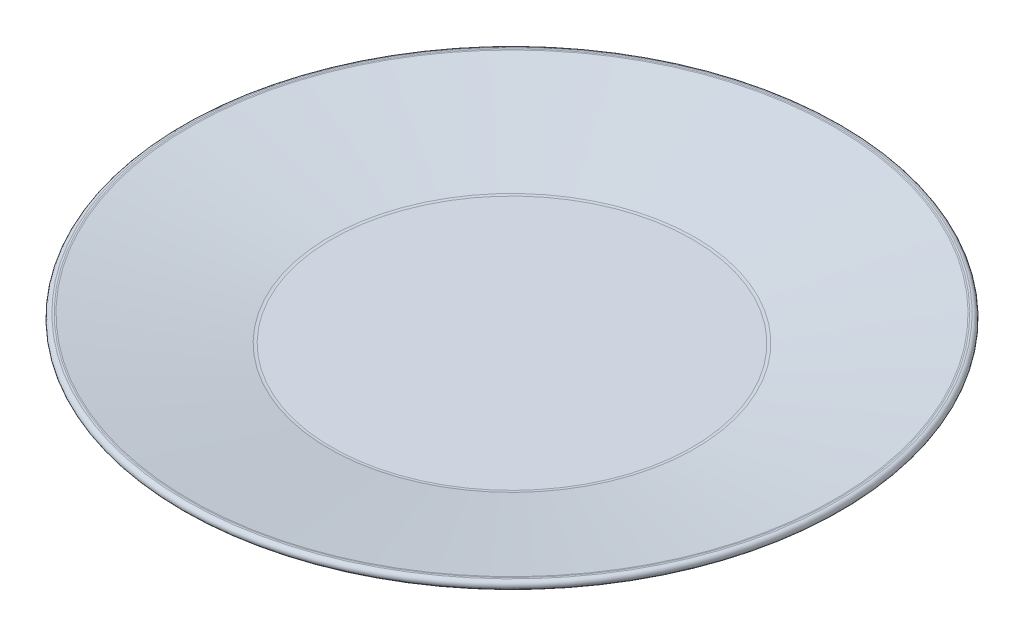
SolidWorks part; units mm, degrees
material "Ceramic Porcelain"
ref_plane "Front Plane" through (0, 0, 0) normal (0, 0, 1) x (1, 0, 0)
ref_plane "Top Plane" through (0, 0, 0) normal (0, 1, 0) x (1, 0, 0)
ref_plane "Right Plane" through (0, 0, 0) normal (1, 0, 0) x (0, 0, -1)
sketch "ProfileS" plane through (0, 0, 0) normal (0, 0, 1) x (1, 0, 0)
  line L0 (0, 0) -> (51.9562, 0)
  line L1 (53.2226, 0.1155) -> (94.0171, 7.6198)
  line L2 (0, 0) -> (0, 10) construction
  line L3 (0, 10) -> (106.9562, 10) construction
  line L4 (0, 2.5) -> (51.9562, 2.5)
  line L5 (52.7703, 2.5743) -> (92.9584, 9.967)
  line L6 (0, 2.5) -> (0, 0)
  line L7 (93.8, 10) -> (93.3202, 10)
  line L8 (53.2226, 0.1155) -> (106.9562, 10) construction
  line L9 (52.7703, 2.5743) -> (106.5039, 12.4587) construction
  line L10 (106.9562, 10) -> (106.9562, 0) construction
  line L11 (106.9562, 0) -> (0, 0) construction
  line L12 (94.0171, 7.6198) -> (106.9562, 10) construction
  line L13 (95, 10) -> (95, 0) construction
  arc A0 (53.2226, 0.1155) -> (51.9562, 0) centre (51.9562, 7) cw
  arc A1 (52.7703, 2.5743) -> (51.9562, 2.5) centre (51.9562, 7) cw
  arc A2 (94.0171, 7.6198) -> (93.8, 10) centre (93.8, 8.8) ccw
  arc A3 (93.3202, 10) -> (92.9584, 9.967) centre (93.3202, 8) ccw
  point P18 (93.1378, 10)
  dimension "SWStartRadius" = 7
  dimension "D1" = 1.2
  dimension "D2" = 2
  dimension "Height" = 10
  dimension "SlantedWallWidth" = 55
  dimension "D3" = 95
  dimension "Thickness" = 2.5
revolve "Profile" add sketch "ProfileS" angle 360 about L2
